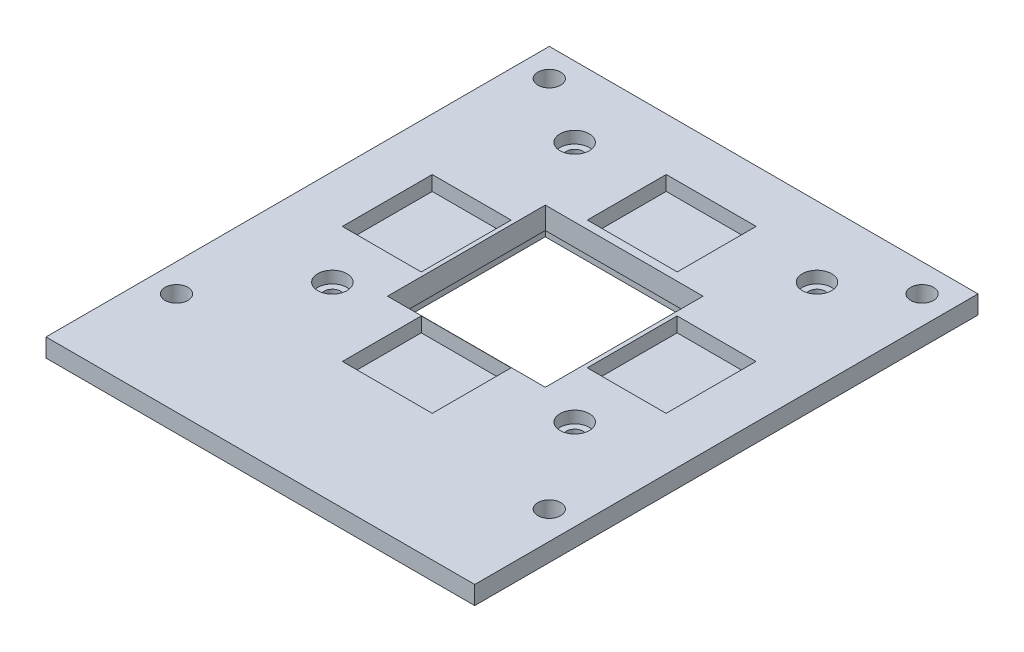
SolidWorks part; units mm, degrees
material "Custom Plastic"
ref_plane "Front Plane" through (0, 0, 0) normal (0, 0, 1) x (1, 0, 0)
ref_plane "Top Plane" through (0, 0, 0) normal (0, 1, 0) x (1, 0, 0)
ref_plane "Right Plane" through (0, 0, 0) normal (1, 0, 0) x (0, 0, -1)
sketch "Sketch1" plane through (0, 0, 0) normal (0, 1, 0) x (1, 0, 0)
  line L1 (-59.1135, 52.1954) -> (57.7265, 52.1954)
  line L2 (-59.1135, 52.1954) -> (-59.1135, -84.9646)
  line L3 (-59.1135, -84.9646) -> (57.7265, -84.9646)
  line L4 (57.7265, 52.1954) -> (57.7265, -84.9646)
  line L5 (-59.1135, 52.1954) -> (57.7265, -84.9646) construction
  line L6 (-59.1135, -84.9646) -> (57.7265, 52.1954) construction
  circle A2 centre (-51.4935, 44.5754) radius 3.1104
  circle A3 centre (50.1065, -57.0246) radius 3.1104
  circle A4 centre (-51.4935, -57.0246) radius 3.1104
  circle A5 centre (50.1065, 44.5754) radius 3.1104
  dimension "D1" = 137.16
  dimension "D2" = 7.62
  dimension "D3" = 7.62
  dimension "D4" = 27.94
  dimension "D5" = 27.94
  dimension "D6" = 7.62
  dimension "D7" = 7.62
  dimension "D8" = 7.62
  dimension "D9" = 7.62
  dimension "D10" = 116.84
extrude "Boss-Extrude1" add sketch "Sketch1" against normal blind 5
sketch "Sketch10" plane through (0, 0, 0) normal (0, 1, 0) x (1, 0, 0)
  line L5 (-22.1955, 14.1927) -> (20.8045, -28.8073) construction
  line L6 (-22.1955, -28.8073) -> (20.8045, 14.1927) construction
  point P0 (-0.6955, -7.3073)
  point P5 (0, 0)
  point P6 (0, 0)
  point P7 (0, 0)
  line B0 (-22.1955, 14.1927) -> (20.8045, 14.1927)
  line B1 (-22.1955, 14.1927) -> (-22.1955, -28.8073)
  line B2 (-22.1955, -28.8073) -> (20.8045, -28.8073)
  line B3 (20.8045, 14.1927) -> (20.8045, -28.8073)
sketch_block_instance "Block1-1"
sketch_block "Block1" parameters "D1"=43, "D2"=43, "D3"=43
sketch "Sketch12" plane through (0, 0, 0) normal (0, 1, 0) x (1, 0, 0)
  line L1 (-42.5, 69.9875) -> (42.5, 69.9875)
  line L2 (-42.5, 69.9875) -> (-42.5, 46.0125)
  line L3 (-42.5, 46.0125) -> (42.5, 46.0125)
  line L4 (42.5, 69.9875) -> (42.5, 46.0125)
  line L5 (-42.5, 69.9875) -> (42.5, 46.0125) construction
  line L6 (-42.5, 46.0125) -> (42.5, 69.9875) construction
  point P0 (0, 58)
extrude "Boss-Extrude15" add sketch "Sketch12" along normal blind 5 separate body
sketch "Sketch13" plane through (0, 0, 0) normal (0, 1, 0) x (1, 0, 0)
  circle A2 centre (33.02, 33.02) radius 2.25
  circle A3 centre (33.02, -33.02) radius 2.25
  circle A4 centre (-33.02, -33.02) radius 2.25
  circle A5 centre (-33.02, 33.02) radius 2.25
sketch "Sketch17" plane through (0, 0, 0) normal (0, 1, 0) x (1, 0, 0)
  line L1 (-25.7, 17.69) -> (24.3, 17.69)
  line L2 (-25.7, 17.69) -> (-25.7, -32.31)
  line L3 (-25.7, -32.31) -> (24.3, -32.31)
  line L4 (24.3, 17.69) -> (24.3, -32.31)
  line L5 (-25.7, 17.69) -> (24.3, -32.31) construction
  line L6 (-25.7, -32.31) -> (24.3, 17.69) construction
  point P0 (-0.7, -7.31)
extrude "Boss-Extrude18" add sketch "Sketch17" against normal blind 6 separate body
extrude "Boss-Extrude19" add sketch "Sketch10" along normal mid plane 50 separate body
sketch "Sketch19" plane through (0, 0, 0) normal (0, 1, 0) x (1, 0, 0)
  line L1 (-28.2, 20.19) -> (26.8, 20.19)
  line L2 (-28.2, 20.19) -> (-28.2, -34.81)
  line L3 (-28.2, -34.81) -> (26.8, -34.81)
  line L4 (26.8, 20.19) -> (26.8, -34.81)
  line L5 (-28.2, 20.19) -> (26.8, -34.81) construction
  line L6 (-28.2, -34.81) -> (26.8, 20.19) construction
  point P0 (-0.7, -7.31)
extrude "Boss-Extrude20" add sketch "Sketch19" against normal blind 11 separate body
combine bodies "Combine1" operation type subtract main body 101 bodies to subtract 136
move or copy body "Body-Move/Copy4" bodies to move or copy 160 copy no translate (0, -6, 0)
combine bodies "Combine4" operation type subtract main body 162 bodies to subtract 164
combine bodies "Combine7" operation type add bodies to combine 167 163
combine bodies "Combine8" operation type subtract main body 168 bodies to subtract 161
sketch "Sketch20" plane through (0, 0, 0) normal (0, 1, 0) x (1, 0, 0)
  circle A2 centre (33.02, 33.02) radius 2.25
  circle A3 centre (33.02, -33.02) radius 2.25
  circle A4 centre (-33.02, -33.02) radius 2.25
  circle A5 centre (-33.02, 33.02) radius 2.25
extrude "Boss-Extrude22" add sketch "Sketch20" along normal mid plane 50 separate body
combine bodies "Combine9" operation type subtract main body 169 bodies to subtract 173 172 171 174
sketch "Sketch21" plane through (0, 0, 0) normal (0, 1, 0) x (1, 0, 0)
  line L1 (-12.94, 37.8954) -> (11.56, 37.8954)
  line L2 (-12.94, 37.8954) -> (-12.94, 16.3954)
  line L3 (-12.94, 16.3954) -> (11.56, 16.3954)
  line L4 (11.56, 37.8954) -> (11.56, 16.3954)
  line L5 (-12.94, 37.8954) -> (11.56, 16.3954) construction
  line L6 (-12.94, 16.3954) -> (11.56, 37.8954) construction
  line L10 (57.7265, 52.1954) -> (-59.1135, 52.1954) construction
  line L11 (-59.1135, -84.9646) -> (57.7265, -84.9646) construction
  line L12 (21.9265, 6) -> (43.4265, 6)
  line L13 (21.9265, 6) -> (21.9265, -18.5)
  line L14 (21.9265, -18.5) -> (43.4265, -18.5)
  line L15 (43.4265, 6) -> (43.4265, -18.5)
  line L16 (21.9265, 6) -> (43.4265, -18.5) construction
  line L17 (21.9265, -18.5) -> (43.4265, 6) construction
  line L18 (-44.8135, 6) -> (-23.3135, 6)
  line L19 (-44.8135, 6) -> (-44.8135, -18.5)
  line L20 (-44.8135, -18.5) -> (-23.3135, -18.5)
  line L21 (-23.3135, 6) -> (-23.3135, -18.5)
  line L22 (-44.8135, 6) -> (-23.3135, -18.5) construction
  line L23 (-44.8135, -18.5) -> (-23.3135, 6) construction
  line L24 (-12.94, -28.8646) -> (11.56, -28.8646)
  line L25 (-12.94, -28.8646) -> (-12.94, -50.3646)
  line L26 (-12.94, -50.3646) -> (11.56, -50.3646)
  line L27 (11.56, -28.8646) -> (11.56, -50.3646)
  line L28 (-12.94, -28.8646) -> (11.56, -50.3646) construction
  line L29 (-12.94, -50.3646) -> (11.56, -28.8646) construction
  line L30 (-59.1135, 52.1954) -> (-59.1135, -84.9646) construction
  line L31 (57.7265, -84.9646) -> (57.7265, 52.1954) construction
  point P0 (-0.69, 27.1454)
  point P11 (32.6765, -6.25)
  point P16 (-34.0635, -6.25)
  point P21 (-0.69, -39.6146)
  dimension "D1" = 14.3
  dimension "D2" = 34.6
  dimension "D3" = 14.3
  dimension "D4" = 14.3
extrude "Boss-Extrude23" add sketch "Sketch21" against normal blind 4 separate body
combine bodies "Combine10" operation type subtract main body 175 bodies to subtract 179 178 177 180
ref_plane "Plane1" through (0, -5, 0) normal (0, -1, 0) x (-1, 0, 0)
sketch "Sketch25" plane through (0, 0, 0) normal (0, 1, 0) x (1, 0, 0)
  circle A0 centre (33.02, 33.02) radius 4
  circle A1 centre (-33.02, 33.02) radius 4
  circle A2 centre (-33.02, -33.02) radius 4
  circle A3 centre (33.02, -33.02) radius 4
extrude "Boss-Extrude24" add sketch "Sketch25" against normal blind 3.25 and the other way blind 10 separate body contours A2 | A0 | A1 | A3
combine bodies "Combine11" operation type subtract main body 181 bodies to subtract 198 200 199 201
